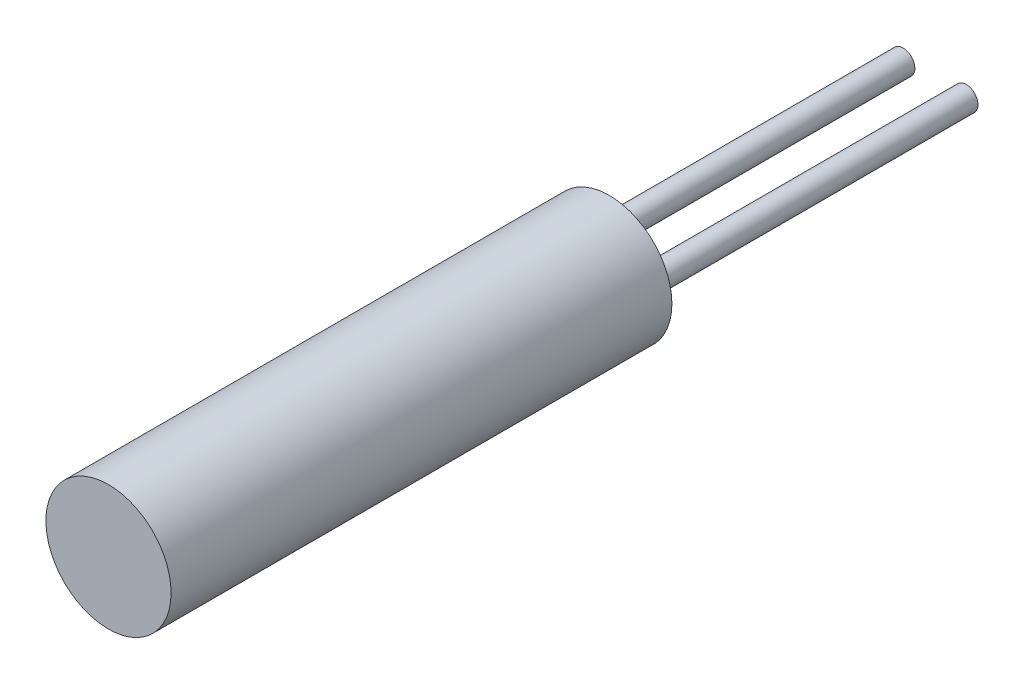
SolidWorks part; units mm, degrees
ref_plane "Front Plane" through (0, 0, 0) normal (0, 0, 1) x (1, 0, 0)
ref_plane "Top Plane" through (0, 0, 0) normal (0, 1, 0) x (1, 0, 0)
ref_plane "Right Plane" through (0, 0, 0) normal (1, 0, 0) x (0, 0, -1)
sketch "Sketch1" plane through (0, 0, 0) normal (0, 0, 1) x (1, 0, 0)
  circle A0 centre (0, 0) radius 3.175
  dimension "D1" = 6.35
extrude "Boss-Extrude1" add sketch "Sketch1" along normal blind 25.4
sketch "Sketch2" plane through (0, 0, 0) normal (0, 0, -1) x (-1, 0, 0)
  line L0 (55, 0) -> (-55, 0) construction
  line L1 (0, 0) -> (0, 3.818) construction
  line L2 (0, 55) -> (0, -55) construction
  line L3 (0, 0) -> (5.2921, 0) construction
  circle A0 centre (-1.6, 0) radius 0.6
  circle A1 centre (1.6, 0) radius 0.6
  dimension "D2" = 1.2
  dimension "D1" = 3.2
extrude "Boss-Extrude2" add sketch "Sketch2" along normal blind 16.5
